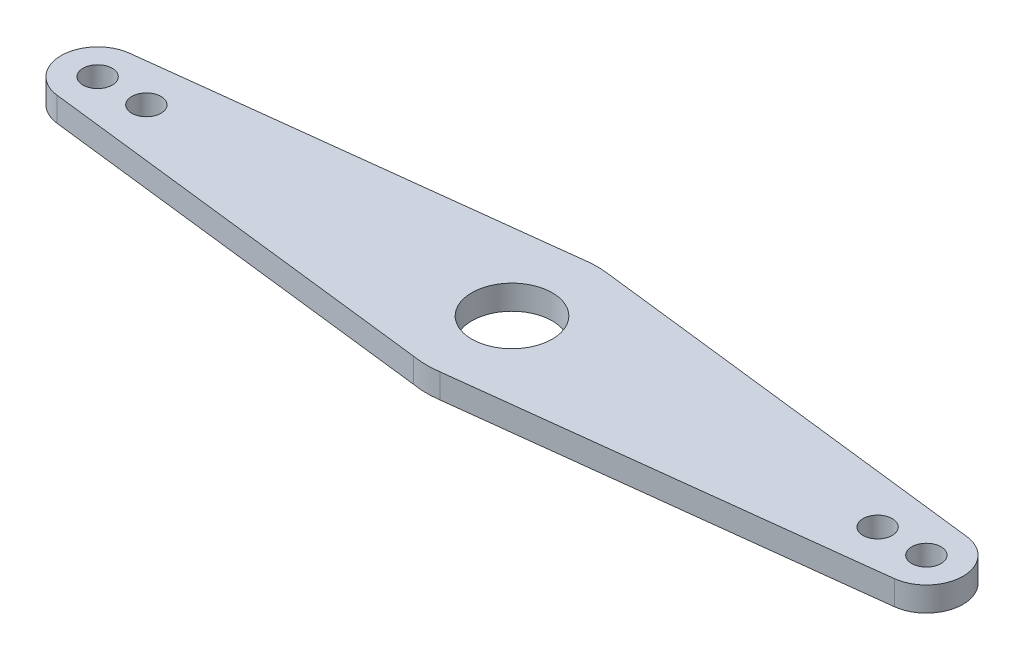
SolidWorks part; units mm, degrees
ref_plane "Front Plane" through (0, 0, 0) normal (0, 0, 1) x (1, 0, 0)
ref_plane "Top Plane" through (0, 0, 0) normal (0, 1, 0) x (1, 0, 0)
ref_plane "Right Plane" through (0, 0, 0) normal (1, 0, 0) x (0, 0, -1)
sketch "Sketch1" plane through (0, 0, 0) normal (0, 1, 0) x (1, 0, 0)
  line L0 (-171.7647, 14.8958) -> (-4.1176, 34.7569)
  line L1 (5.1187, -34.6237) -> (171.7634, -14.896)
  line L2 (4.1176, 34.7569) -> (171.7647, 14.8958)
  line L3 (-6.0367, -34.4755) -> (-171.7599, -14.8964)
  arc A0 (-6.0367, -34.4755) -> (5.1187, -34.6237) centre (0, 0) ccw
  arc A1 (-171.7647, 14.8958) -> (-171.7599, -14.8964) centre (-170, 0) ccw
  arc A2 (171.7634, -14.896) -> (171.7647, 14.8958) centre (170, 0) ccw
  arc A3 (4.1176, 34.7569) -> (-4.1176, 34.7569) centre (0, 0) ccw
  dimension "D1" = 30
  dimension "D2" = 30
  dimension "D3" = 70
  dimension "D4" = 170
  dimension "D5" = 170
  dimension "D6" = 170
  dimension "D7" = 170
extrude "Boss-Extrude2" add sketch "Sketch1" along normal blind 10
sketch "Sketch3" plane through (0, 10, 0) normal (0, 1, 0) x (1, 0, 0)
  circle A0 centre (170, 0) radius 6
  circle A1 centre (-170, 0) radius 6
  circle A2 centre (-150, 0) radius 6
  circle A3 centre (150, 0) radius 6
  dimension "D1" = 12
  dimension "D2" = 12
  dimension "D3" = 12
  dimension "D4" = 12
  dimension "D5" = 20
  dimension "D6" = 20
extrude "Cut-Extrude1" cut sketch "Sketch3" against normal blind 10
sketch "Sketch4" plane through (0, 10, 0) normal (0, 1, 0) x (1, 0, 0)
  circle A0 centre (0, 0) radius 16.5
  dimension "D1" = 33
extrude "Cut-Extrude2" cut sketch "Sketch4" against normal blind 10
